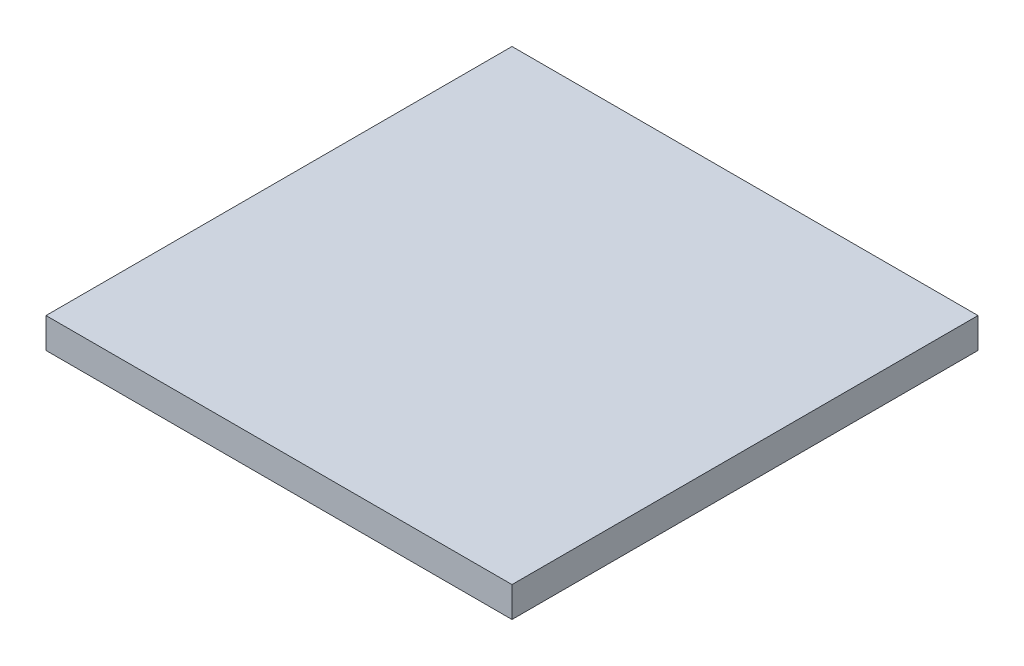
SolidWorks part; units mm, degrees
ref_plane "Front Plane" through (0, 0, 0) normal (0, 0, 1) x (1, 0, 0)
ref_plane "Top Plane" through (0, 0, 0) normal (0, 1, 0) x (1, 0, 0)
ref_plane "Right Plane" through (0, 0, 0) normal (1, 0, 0) x (0, 0, -1)
sketch "Sketch1" plane through (0, 0, 0) normal (0, 1, 0) x (1, 0, 0)
  line L1 (-2925, 2925) -> (2925, 2925)
  line L2 (-2925, 2925) -> (-2925, -2925)
  line L3 (-2925, -2925) -> (2925, -2925)
  line L4 (2925, 2925) -> (2925, -2925)
  line L5 (-2925, 2925) -> (2925, -2925) construction
  line L6 (-2925, -2925) -> (2925, 2925) construction
  point P0 (0, 0)
  dimension "D1" = 5850
  dimension "D2" = 5850
extrude "Boss-Extrude1" add sketch "Sketch1" along normal blind 380
sketch "Sketch2" plane through (0, 0, 0) normal (0, -1, 0) x (1, 0, 0)
  line L0 (0, 0) -> (-834.4991, 0)
  circle A0 centre (0, 0) radius 200
